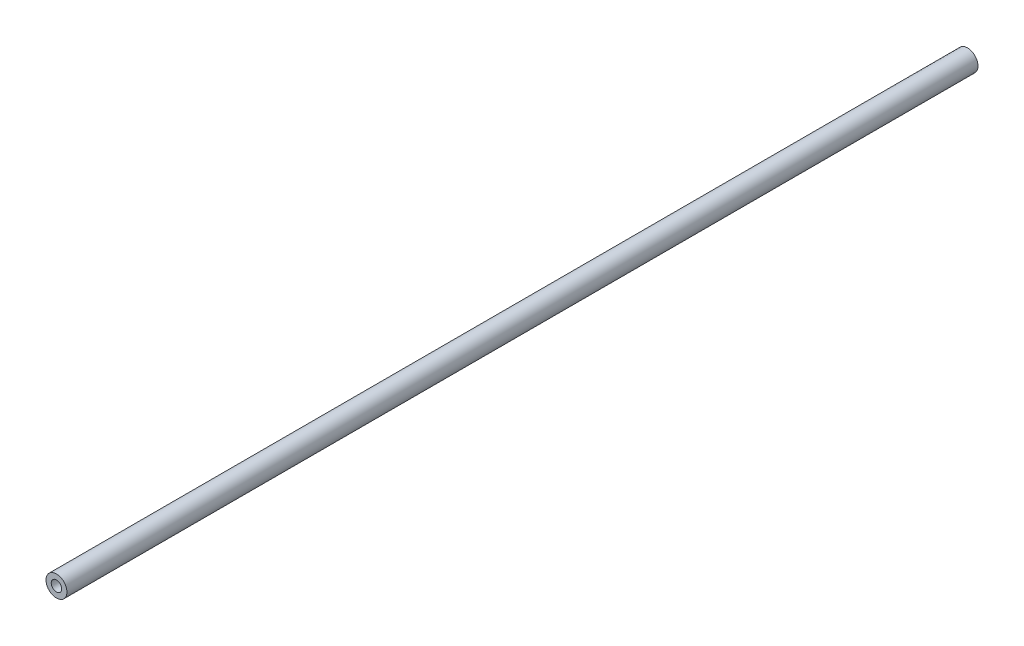
SolidWorks part; units mm, degrees
material "6061-T6 (SS)"
ref_plane "Plan de face" through (0, 0, 0) normal (0, 0, 1) x (1, 0, 0)
ref_plane "Plan de dessus" through (0, 0, 0) normal (0, 1, 0) x (1, 0, 0)
ref_plane "Plan de droite" through (0, 0, 0) normal (1, 0, 0) x (0, 0, -1)
sketch "Esquisse1" plane through (0, 0, 0) normal (0, 0, 1) x (1, 0, 0)
  circle A0 centre (0, 0) radius 12.7
  circle A1 centre (0, 0) radius 6.35
  dimension "D1" = 6.35
  dimension "D2" = 25.4
extrude "Boss.-Extru.1" add sketch "Esquisse1" along normal blind 1104.9
